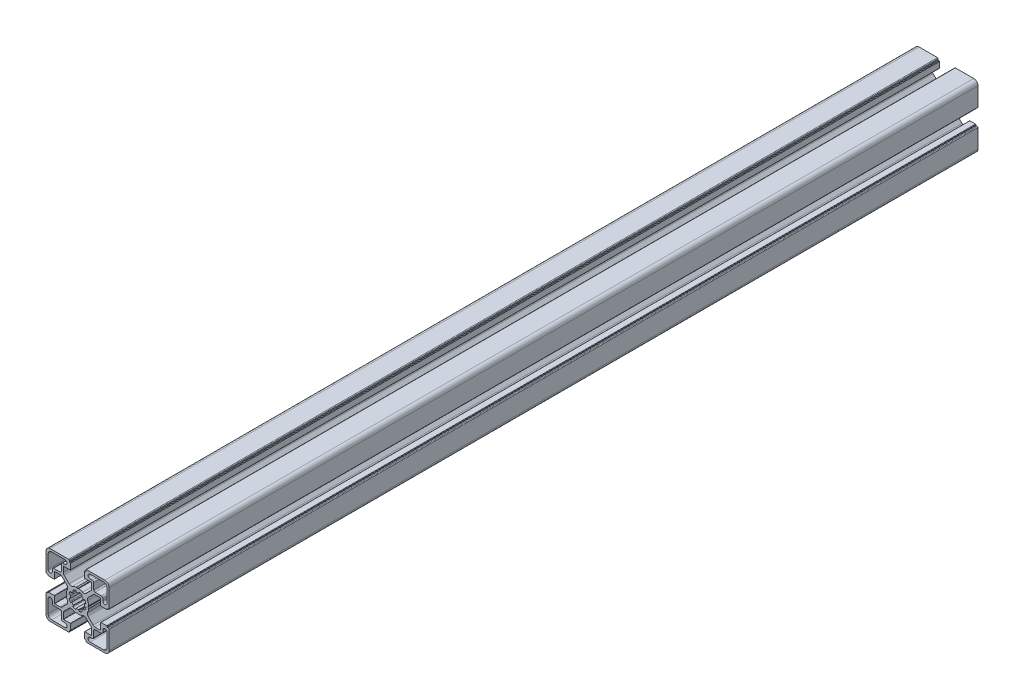
SolidWorks part; units mm, degrees
ref_plane "Front Plane" through (0, 0, 0) normal (0, 0, 1) x (1, 0, 0)
ref_plane "Top Plane" through (0, 0, 0) normal (0, 1, 0) x (1, 0, 0)
ref_plane "Right Plane" through (0, 0, 0) normal (1, 0, 0) x (0, 0, -1)
sketch "Sketch1" plane through (0, 0, 0) normal (0, 0, 1) x (1, 0, 0)
  line L0 (10.55, 18) -> (9, 18)
  line L1 (18.5, 21) -> (9, 21)
  line L2 (21, 9.0002) -> (21, 18.5)
  line L3 (18, 9.0002) -> (18, 10.55)
  line L4 (17, 11.55) -> (12.55, 11.55)
  line L5 (11.55, 12.55) -> (11.55, 17)
  line L6 (7.974, 0.7926) -> (7.5401, 0.0468)
  line L7 (-0.8674, 4.9242) -> (-0.9675, 5.4811)
  line L8 (-3.1913, 4.5626) -> (-2.864, 4.0985)
  line L9 (-4.0897, 2.8765) -> (-4.5668, 3.2082)
  line L10 (-5.4897, 0.9862) -> (-4.9205, 0.8878)
  line L11 (11.1298, 9.425) -> (7.5635, 5.8587)
  line L12 (16.3169, 9.9945) -> (12.5048, 9.9945)
  line L13 (16.5169, 5.2) -> (16.5169, 9.7945)
  line L14 (20.7196, 5) -> (16.7169, 5)
  line L15 (21.0196, 5.3) -> (21.0196, 5.5)
  line L16 (22, 5.8) -> (21.3196, 5.8)
  line L17 (22.5, 6.3) -> (22.5, 19.5)
  line L18 (19.5, 22.5) -> (6.3757, 22.5)
  line L19 (5.8757, 21.3) -> (5.8757, 22)
  line L20 (5.5757, 21) -> (5.3, 21)
  line L21 (5, 16.6668) -> (5, 20.7)
  line L22 (9.9054, 16.4668) -> (5.2, 16.4668)
  line L23 (10.1054, 12.4716) -> (10.1054, 16.2668)
  line L24 (5.9449, 7.4827) -> (9.5196, 11.0574)
  line L25 (0.1126, 7.6069) -> (0.7547, 7.9748)
  line L26 (5.4897, 0.9862) -> (4.9205, 0.8878)
  line L27 (4.0897, 2.8765) -> (4.5668, 3.2082)
  line L28 (3.1913, 4.5626) -> (2.864, 4.0985)
  line L29 (0.8674, 4.9242) -> (0.9675, 5.4811)
  line L30 (-10.55, -18) -> (-9, -18)
  line L31 (-18.5, -21) -> (-9, -21)
  line L32 (-21, -9.0002) -> (-21, -18.5)
  line L33 (-18, -9.0002) -> (-18, -10.55)
  line L34 (-17, -11.55) -> (-12.55, -11.55)
  line L35 (-11.55, -12.55) -> (-11.55, -17)
  line L36 (-7.974, -0.7926) -> (-7.5401, -0.0468)
  line L37 (-11.1298, -9.425) -> (-7.5635, -5.8587)
  line L38 (-16.3169, -9.9945) -> (-12.5048, -9.9945)
  line L39 (-16.5169, -5.2) -> (-16.5169, -9.7945)
  line L40 (-20.7196, -5) -> (-16.7169, -5)
  line L41 (-21.0196, -5.3) -> (-21.0196, -5.5)
  line L42 (-22, -5.8) -> (-21.3196, -5.8)
  line L43 (-22.5, -6.3) -> (-22.5, -19.5)
  line L44 (-19.5, -22.5) -> (-6.3757, -22.5)
  line L45 (-5.8757, -21.3) -> (-5.8757, -22)
  line L46 (-5.5757, -21) -> (-5.3, -21)
  line L47 (-5, -16.6668) -> (-5, -20.7)
  line L48 (-9.9054, -16.4668) -> (-5.2, -16.4668)
  line L49 (-10.1054, -12.4716) -> (-10.1054, -16.2668)
  line L50 (-5.9449, -7.4827) -> (-9.5196, -11.0574)
  line L51 (-0.1126, -7.6069) -> (-0.7547, -7.9748)
  line L52 (0.8674, -4.9242) -> (0.9675, -5.4811)
  line L53 (3.1913, -4.5626) -> (2.864, -4.0985)
  line L54 (4.0897, -2.8765) -> (4.5668, -3.2082)
  line L55 (5.4897, -0.9862) -> (4.9205, -0.8878)
  line L56 (0.1126, -7.6069) -> (0.7547, -7.9748)
  line L57 (5.9449, -7.4827) -> (9.5196, -11.0574)
  line L58 (10.1054, -12.4716) -> (10.1054, -16.2668)
  line L59 (9.9054, -16.4668) -> (5.2, -16.4668)
  line L60 (5, -16.6668) -> (5, -20.7)
  line L61 (5.5757, -21) -> (5.3, -21)
  line L62 (-0.1126, 7.6069) -> (-0.7547, 7.9748)
  line L63 (-5.9449, 7.4827) -> (-9.5196, 11.0574)
  line L64 (-10.1054, 12.4716) -> (-10.1054, 16.2668)
  line L65 (-9.9054, 16.4668) -> (-5.2, 16.4668)
  line L66 (-5, 16.6668) -> (-5, 20.7)
  line L67 (-5.5757, 21) -> (-5.3, 21)
  line L68 (-5.8757, 21.3) -> (-5.8757, 22)
  line L69 (-19.5, 22.5) -> (-6.3757, 22.5)
  line L70 (-22.5, 6.3) -> (-22.5, 19.5)
  line L71 (-22, 5.8) -> (-21.3196, 5.8)
  line L72 (-21.0196, 5.3) -> (-21.0196, 5.5)
  line L73 (-20.7196, 5) -> (-16.7169, 5)
  line L74 (-16.5169, 5.2) -> (-16.5169, 9.7945)
  line L75 (-16.3169, 9.9945) -> (-12.5048, 9.9945)
  line L76 (-11.1298, 9.425) -> (-7.5635, 5.8587)
  line L77 (-7.974, 0.7926) -> (-7.5401, 0.0468)
  line L78 (5.8757, -21.3) -> (5.8757, -22)
  line L79 (19.5, -22.5) -> (6.3757, -22.5)
  line L80 (22.5, -6.3) -> (22.5, -19.5)
  line L81 (22, -5.8) -> (21.3196, -5.8)
  line L82 (21.0196, -5.3) -> (21.0196, -5.5)
  line L83 (20.7196, -5) -> (16.7169, -5)
  line L84 (16.5169, -5.2) -> (16.5169, -9.7945)
  line L85 (16.3169, -9.9945) -> (12.5048, -9.9945)
  line L86 (11.1298, -9.425) -> (7.5635, -5.8587)
  line L87 (-5.4897, -0.9862) -> (-4.9205, -0.8878)
  line L88 (-4.0897, -2.8765) -> (-4.5668, -3.2082)
  line L89 (-3.1913, -4.5626) -> (-2.864, -4.0985)
  line L90 (-0.8674, -4.9242) -> (-0.9675, -5.4811)
  line L91 (7.974, -0.7926) -> (7.5401, -0.0468)
  line L92 (-11.55, 12.55) -> (-11.55, 17)
  line L93 (-17, 11.55) -> (-12.55, 11.55)
  line L94 (-18, 9.0002) -> (-18, 10.55)
  line L95 (-21, 9.0002) -> (-21, 18.5)
  line L96 (-18.5, 21) -> (-9, 21)
  line L97 (-10.55, 18) -> (-9, 18)
  line L98 (11.55, -12.55) -> (11.55, -17)
  line L99 (17, -11.55) -> (12.55, -11.55)
  line L100 (18, -9.0002) -> (18, -10.55)
  line L101 (21, -9.0002) -> (21, -18.5)
  line L102 (18.5, -21) -> (9, -21)
  line L103 (10.55, -18) -> (9, -18)
  line L104 (-33.3633, 0) -> (37.7265, 0) construction
  line L105 (0, 32.2957) -> (0, -36.0465) construction
  arc A0 (9, 18) -> (9, 21) centre (9, 19.5) cw
  arc A1 (18.5, 21) -> (21, 18.5) centre (18.5, 18.5) cw
  arc A2 (21, 9.0002) -> (18, 9.0002) centre (19.5, 9.0002) cw
  arc A3 (17, 11.55) -> (18, 10.55) centre (17, 10.55) cw
  arc A4 (12.55, 11.55) -> (11.55, 12.55) centre (12.55, 12.55) cw
  arc A5 (10.55, 18) -> (11.55, 17) centre (10.55, 17) cw
  arc A6 (7.5313, 0) -> (7.5401, 0.0468) centre (7.7309, -0.013) cw
  arc A7 (8, 0.9141) -> (7.974, 0.7926) centre (7.8011, 0.8932) cw
  arc A8 (7.2004, 3.6119) -> (8, 0.9141) centre (0.0496, 0.0249) cw
  arc A9 (7.2004, 3.6119) -> (7.5635, 5.8587) centre (8.9385, 4.4837) cw
  arc A10 (11.1298, 9.425) -> (12.5048, 9.9945) centre (12.5048, 8.05) cw
  arc A11 (16.3169, 9.9945) -> (16.5169, 9.7945) centre (16.3169, 9.7945) cw
  arc A12 (16.7169, 5) -> (16.5169, 5.2) centre (16.7169, 5.2) cw
  arc A13 (21.0196, 5.3) -> (20.7196, 5) centre (20.7196, 5.3) cw
  arc A14 (0.8674, 4.9242) -> (-0.8674, 4.9242) centre (0, 0) ccw
  arc A15 (-0.9675, 5.4811) -> (-1.5951, 5.8941) centre (-1.4627, 5.4119) ccw
  arc A16 (-1.5951, 5.8941) -> (-3.0444, 5.2994) centre (-0.0235, 0) ccw
  arc A17 (-3.0444, 5.2994) -> (-3.1913, 4.5626) centre (-2.7943, 4.8665) ccw
  arc A18 (-2.864, 4.0985) -> (-4.0897, 2.8765) centre (0, 0) ccw
  arc A19 (-4.5668, 3.2082) -> (-5.3025, 3.0565) centre (-4.868, 2.8091) ccw
  arc A20 (-5.3025, 3.0565) -> (-5.9068, 1.6112) centre (-0.0235, 0) ccw
  arc A21 (-5.9068, 1.6112) -> (-5.4897, 0.9862) centre (-5.4239, 1.4819) ccw
  arc A22 (-4.9205, 0.8878) -> (-5, 0) centre (0, 0) ccw
  arc A23 (21.0196, 5.5) -> (21.3196, 5.8) centre (21.3196, 5.5) cw
  arc A24 (22.5, 6.3) -> (22, 5.8) centre (22, 6.3) cw
  arc A25 (19.5, 22.5) -> (22.5, 19.5) centre (19.5, 19.5) cw
  arc A26 (5.8757, 22) -> (6.3757, 22.5) centre (6.3757, 22) cw
  arc A27 (5.8757, 21.3) -> (5.5757, 21) centre (5.5757, 21.3) cw
  arc A28 (5, 20.7) -> (5.3, 21) centre (5.3, 20.7) cw
  arc A29 (5.2, 16.4668) -> (5, 16.6668) centre (5.2, 16.6668) cw
  arc A30 (9.9054, 16.4668) -> (10.1054, 16.2668) centre (9.9054, 16.2668) cw
  arc A31 (10.1054, 12.4716) -> (9.5196, 11.0574) centre (8.1054, 12.4716) cw
  arc A32 (5.9449, 7.4827) -> (3.6665, 7.1733) centre (4.5855, 8.9496) cw
  arc A33 (0.8764, 8) -> (3.6665, 7.1733) centre (0.0235, 0) cw
  arc A34 (0.7547, 7.9748) -> (0.8764, 8) centre (0.8542, 7.8013) cw
  arc A35 (0.1126, 7.6069) -> (0, 7.531) centre (-0.0489, 7.7249) cw
  arc A36 (4.9205, 0.8878) -> (5, 0) centre (0, 0) cw
  arc A37 (5.9068, 1.6112) -> (5.4897, 0.9862) centre (5.4239, 1.4819) cw
  arc A38 (5.3025, 3.0565) -> (5.9068, 1.6112) centre (0.0235, 0) cw
  arc A39 (4.5668, 3.2082) -> (5.3025, 3.0565) centre (4.868, 2.8091) cw
  arc A40 (2.864, 4.0985) -> (4.0897, 2.8765) centre (0, 0) cw
  arc A41 (3.0444, 5.2994) -> (3.1913, 4.5626) centre (2.7943, 4.8665) cw
  arc A42 (1.5951, 5.8941) -> (3.0444, 5.2994) centre (0.0235, 0) cw
  arc A43 (0.9675, 5.4811) -> (1.5951, 5.8941) centre (1.4627, 5.4119) cw
  arc A44 (-9, -18) -> (-9, -21) centre (-9, -19.5) cw
  arc A45 (-18.5, -21) -> (-21, -18.5) centre (-18.5, -18.5) cw
  arc A46 (-21, -9.0002) -> (-18, -9.0002) centre (-19.5, -9.0002) cw
  arc A47 (-17, -11.55) -> (-18, -10.55) centre (-17, -10.55) cw
  arc A48 (-12.55, -11.55) -> (-11.55, -12.55) centre (-12.55, -12.55) cw
  arc A49 (-10.55, -18) -> (-11.55, -17) centre (-10.55, -17) cw
  arc A50 (-7.5313, 0) -> (-7.5401, -0.0468) centre (-7.7309, 0.013) cw
  arc A51 (-8, -0.9141) -> (-7.974, -0.7926) centre (-7.8011, -0.8932) cw
  arc A52 (-7.2004, -3.6119) -> (-8, -0.9141) centre (-0.0496, -0.0249) cw
  arc A53 (-7.2004, -3.6119) -> (-7.5635, -5.8587) centre (-8.9385, -4.4837) cw
  arc A54 (-11.1298, -9.425) -> (-12.5048, -9.9945) centre (-12.5048, -8.05) cw
  arc A55 (-16.3169, -9.9945) -> (-16.5169, -9.7945) centre (-16.3169, -9.7945) cw
  arc A56 (-16.7169, -5) -> (-16.5169, -5.2) centre (-16.7169, -5.2) cw
  arc A57 (-21.0196, -5.3) -> (-20.7196, -5) centre (-20.7196, -5.3) cw
  arc A58 (-21.0196, -5.5) -> (-21.3196, -5.8) centre (-21.3196, -5.5) cw
  arc A59 (-22.5, -6.3) -> (-22, -5.8) centre (-22, -6.3) cw
  arc A60 (-19.5, -22.5) -> (-22.5, -19.5) centre (-19.5, -19.5) cw
  arc A61 (-5.8757, -22) -> (-6.3757, -22.5) centre (-6.3757, -22) cw
  arc A62 (-5.8757, -21.3) -> (-5.5757, -21) centre (-5.5757, -21.3) cw
  arc A63 (-5, -20.7) -> (-5.3, -21) centre (-5.3, -20.7) cw
  arc A64 (-5.2, -16.4668) -> (-5, -16.6668) centre (-5.2, -16.6668) cw
  arc A65 (-9.9054, -16.4668) -> (-10.1054, -16.2668) centre (-9.9054, -16.2668) cw
  arc A66 (-10.1054, -12.4716) -> (-9.5196, -11.0574) centre (-8.1054, -12.4716) cw
  arc A67 (-5.9449, -7.4827) -> (-3.6665, -7.1733) centre (-4.5855, -8.9496) cw
  arc A68 (-0.8764, -8) -> (-3.6665, -7.1733) centre (-0.0235, 0) cw
  arc A69 (-0.7547, -7.9748) -> (-0.8764, -8) centre (-0.8542, -7.8013) cw
  arc A70 (-0.1126, -7.6069) -> (0, -7.531) centre (0.0489, -7.7249) cw
  arc A71 (0.9675, -5.4811) -> (1.5951, -5.8941) centre (1.4627, -5.4119) ccw
  arc A72 (1.5951, -5.8941) -> (3.0444, -5.2994) centre (0.0235, 0) ccw
  arc A73 (3.0444, -5.2994) -> (3.1913, -4.5626) centre (2.7943, -4.8665) ccw
  arc A74 (2.864, -4.0985) -> (4.0897, -2.8765) centre (0, 0) ccw
  arc A75 (4.5668, -3.2082) -> (5.3025, -3.0565) centre (4.868, -2.8091) ccw
  arc A76 (5.3025, -3.0565) -> (5.9068, -1.6112) centre (0.0235, 0) ccw
  arc A77 (5.9068, -1.6112) -> (5.4897, -0.9862) centre (5.4239, -1.4819) ccw
  arc A78 (4.9205, -0.8878) -> (5, 0) centre (0, 0) ccw
  arc A79 (0.1126, -7.6069) -> (0, -7.531) centre (-0.0489, -7.7249) ccw
  arc A80 (0.7547, -7.9748) -> (0.8764, -8) centre (0.8542, -7.8013) ccw
  arc A81 (0.8764, -8) -> (3.6665, -7.1733) centre (0.0235, 0) ccw
  arc A82 (5.9449, -7.4827) -> (3.6665, -7.1733) centre (4.5855, -8.9496) ccw
  arc A83 (10.1054, -12.4716) -> (9.5196, -11.0574) centre (8.1054, -12.4716) ccw
  arc A84 (9.9054, -16.4668) -> (10.1054, -16.2668) centre (9.9054, -16.2668) ccw
  arc A85 (5.2, -16.4668) -> (5, -16.6668) centre (5.2, -16.6668) ccw
  arc A86 (5, -20.7) -> (5.3, -21) centre (5.3, -20.7) ccw
  arc A87 (5.8757, -21.3) -> (5.5757, -21) centre (5.5757, -21.3) ccw
  arc A88 (-0.1126, 7.6069) -> (0, 7.531) centre (0.0489, 7.7249) ccw
  arc A89 (-0.7547, 7.9748) -> (-0.8764, 8) centre (-0.8542, 7.8013) ccw
  arc A90 (-0.8764, 8) -> (-3.6665, 7.1733) centre (-0.0235, 0) ccw
  arc A91 (-5.9449, 7.4827) -> (-3.6665, 7.1733) centre (-4.5855, 8.9496) ccw
  arc A92 (-10.1054, 12.4716) -> (-9.5196, 11.0574) centre (-8.1054, 12.4716) ccw
  arc A93 (-9.9054, 16.4668) -> (-10.1054, 16.2668) centre (-9.9054, 16.2668) ccw
  arc A94 (-5.2, 16.4668) -> (-5, 16.6668) centre (-5.2, 16.6668) ccw
  arc A95 (-5, 20.7) -> (-5.3, 21) centre (-5.3, 20.7) ccw
  arc A96 (-5.8757, 21.3) -> (-5.5757, 21) centre (-5.5757, 21.3) ccw
  arc A97 (-5.8757, 22) -> (-6.3757, 22.5) centre (-6.3757, 22) ccw
  arc A98 (-19.5, 22.5) -> (-22.5, 19.5) centre (-19.5, 19.5) ccw
  arc A99 (-22.5, 6.3) -> (-22, 5.8) centre (-22, 6.3) ccw
  arc A100 (-21.0196, 5.5) -> (-21.3196, 5.8) centre (-21.3196, 5.5) ccw
  arc A101 (-21.0196, 5.3) -> (-20.7196, 5) centre (-20.7196, 5.3) ccw
  arc A102 (-16.7169, 5) -> (-16.5169, 5.2) centre (-16.7169, 5.2) ccw
  arc A103 (-16.3169, 9.9945) -> (-16.5169, 9.7945) centre (-16.3169, 9.7945) ccw
  arc A104 (-11.1298, 9.425) -> (-12.5048, 9.9945) centre (-12.5048, 8.05) ccw
  arc A105 (-7.2004, 3.6119) -> (-7.5635, 5.8587) centre (-8.9385, 4.4837) ccw
  arc A106 (-7.2004, 3.6119) -> (-8, 0.9141) centre (-0.0496, 0.0249) ccw
  arc A107 (-8, 0.9141) -> (-7.974, 0.7926) centre (-7.8011, 0.8932) ccw
  arc A108 (-7.5313, 0) -> (-7.5401, 0.0468) centre (-7.7309, -0.013) ccw
  arc A109 (5.8757, -22) -> (6.3757, -22.5) centre (6.3757, -22) ccw
  arc A110 (19.5, -22.5) -> (22.5, -19.5) centre (19.5, -19.5) ccw
  arc A111 (22.5, -6.3) -> (22, -5.8) centre (22, -6.3) ccw
  arc A112 (21.0196, -5.5) -> (21.3196, -5.8) centre (21.3196, -5.5) ccw
  arc A113 (-4.9205, -0.8878) -> (-5, 0) centre (0, 0) cw
  arc A114 (-5.9068, -1.6112) -> (-5.4897, -0.9862) centre (-5.4239, -1.4819) cw
  arc A115 (-5.3025, -3.0565) -> (-5.9068, -1.6112) centre (-0.0235, 0) cw
  arc A116 (-4.5668, -3.2082) -> (-5.3025, -3.0565) centre (-4.868, -2.8091) cw
  arc A117 (-2.864, -4.0985) -> (-4.0897, -2.8765) centre (0, 0) cw
  arc A118 (-3.0444, -5.2994) -> (-3.1913, -4.5626) centre (-2.7943, -4.8665) cw
  arc A119 (-1.5951, -5.8941) -> (-3.0444, -5.2994) centre (-0.0235, 0) cw
  arc A120 (-0.9675, -5.4811) -> (-1.5951, -5.8941) centre (-1.4627, -5.4119) cw
  arc A121 (0.8674, -4.9242) -> (-0.8674, -4.9242) centre (0, 0) cw
  arc A122 (21.0196, -5.3) -> (20.7196, -5) centre (20.7196, -5.3) ccw
  arc A123 (16.7169, -5) -> (16.5169, -5.2) centre (16.7169, -5.2) ccw
  arc A124 (-10.55, 18) -> (-11.55, 17) centre (-10.55, 17) ccw
  arc A125 (-12.55, 11.55) -> (-11.55, 12.55) centre (-12.55, 12.55) ccw
  arc A126 (-17, 11.55) -> (-18, 10.55) centre (-17, 10.55) ccw
  arc A127 (-21, 9.0002) -> (-18, 9.0002) centre (-19.5, 9.0002) ccw
  arc A128 (-18.5, 21) -> (-21, 18.5) centre (-18.5, 18.5) ccw
  arc A129 (-9, 18) -> (-9, 21) centre (-9, 19.5) ccw
  arc A130 (16.3169, -9.9945) -> (16.5169, -9.7945) centre (16.3169, -9.7945) ccw
  arc A131 (11.1298, -9.425) -> (12.5048, -9.9945) centre (12.5048, -8.05) ccw
  arc A132 (7.2004, -3.6119) -> (7.5635, -5.8587) centre (8.9385, -4.4837) ccw
  arc A133 (7.2004, -3.6119) -> (8, -0.9141) centre (0.0496, -0.0249) ccw
  arc A134 (8, -0.9141) -> (7.974, -0.7926) centre (7.8011, -0.8932) ccw
  arc A135 (7.5313, 0) -> (7.5401, -0.0468) centre (7.7309, 0.013) ccw
  arc A136 (10.55, -18) -> (11.55, -17) centre (10.55, -17) ccw
  arc A137 (12.55, -11.55) -> (11.55, -12.55) centre (12.55, -12.55) ccw
  arc A138 (17, -11.55) -> (18, -10.55) centre (17, -10.55) ccw
  arc A139 (21, -9.0002) -> (18, -9.0002) centre (19.5, -9.0002) ccw
  arc A140 (18.5, -21) -> (21, -18.5) centre (18.5, -18.5) ccw
  arc A141 (9, -18) -> (9, -21) centre (9, -19.5) ccw
  dimension "D6" = 12.2
  dimension "D8" = 10
  dimension "D1" = 10
  dimension "D2" = 45
  dimension "D3" = 45
  dimension "D4" = 10
  dimension "D5" = 14.5
  dimension "D7" = 22.5
extrude "Base-Extrude" add sketch "Sketch1" against normal blind 620
